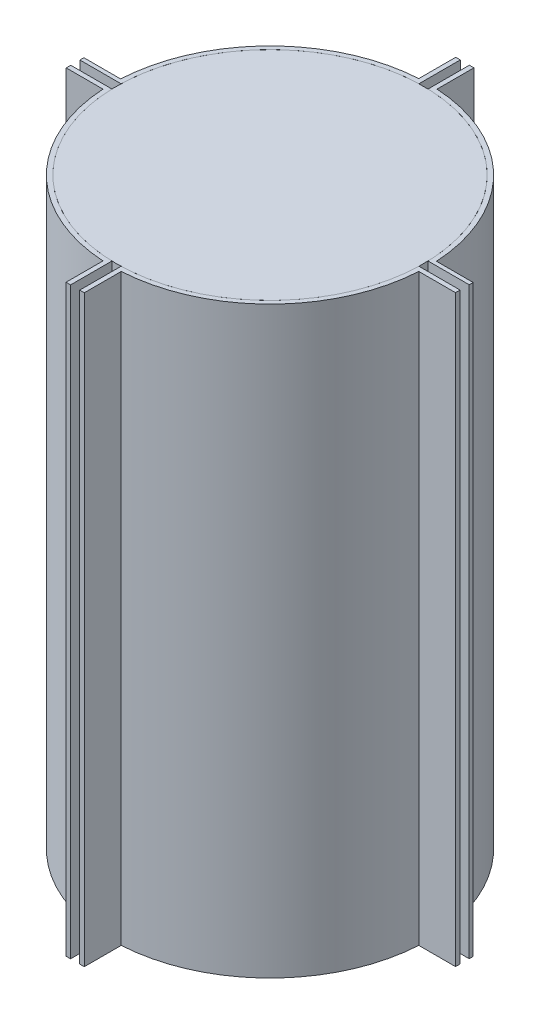
SolidWorks part; units mm, degrees
material "Alumina"
ref_plane "Front Plane" through (0, 0, 0) normal (0, 0, 1) x (1, 0, 0)
ref_plane "Top Plane" through (0, 0, 0) normal (0, 1, 0) x (1, 0, 0)
ref_plane "Right Plane" through (0, 0, 0) normal (1, 0, 0) x (0, 0, -1)
sketch "Sketch1" plane through (0, 0, 0) normal (0, 1, 0) x (1, 0, 0)
  circle A0 centre (0, 0) radius 106.934
extrude "Boss-Extrude1" add sketch "Sketch1" along normal blind 406.4
sketch "Sketch2" plane through (0, 0, 0) normal (0, 1, 0) x (1, 0, 0)
  line L1 (-110.109, 0) -> (110.109, 0) construction
  line L2 (0, 110.109) -> (0, -110.109) construction
  arc A0 (106.934, 0) -> (0, 106.934) centre (0, 0) ccw
  circle A1 centre (0, 0) radius 106.934 construction
  arc A2 (0, 106.934) -> (-106.934, 0) centre (0, 0) ccw
  arc A3 (106.934, 0) -> (0, -106.934) centre (0, 0) cw
  arc A4 (0, -106.934) -> (-106.934, 0) centre (0, 0) cw
  arc A6 (110.109, 0) -> (0, 110.109) centre (0, 0) ccw
  arc A7 (0, 110.109) -> (-110.109, 0) centre (0, 0) ccw
  arc A8 (-110.109, 0) -> (0, -110.109) centre (0, 0) ccw
  arc A9 (0, -110.109) -> (110.109, 0) centre (0, 0) ccw
  point P9 (110.109, 0)
sketch "Sketch3" plane through (0, 0, 0) normal (0, 1, 0) x (1, 0, 0)
  line L0 (0, 110.109) -> (0, -110.109) construction
  line L1 (-127, 3.175) -> (127, 3.175)
  line L2 (0, 3.175) -> (0, -3.175)
  line L3 (-127, -3.175) -> (127, -3.175)
  line L4 (127, 3.175) -> (127, -3.175)
  line L5 (-110.109, 0) -> (110.109, 0) construction
  line L6 (-127, 3.175) -> (-127, -3.175)
  line L7 (-3.175, -127) -> (3.175, -127)
  line L11 (-3.175, 0) -> (3.175, 0)
  line L12 (-3.175, -127) -> (-3.175, 127)
  line L13 (-3.175, 127) -> (3.175, 127)
  line L14 (3.175, -127) -> (3.175, 127)
  point P18 (0, 121.6953)
  dimension "D1" = 6.35
  dimension "D2" = 254
  dimension "D3" = 254
  dimension "D4" = 6.35
  dimension "D5" = 123.825
  dimension "D6" = 123.825
extrude "Boss-Extrude3" add sketch "Sketch2" along normal blind 406.4 separate body
extrude "Cut-Extrude2" cut sketch "Sketch3" along normal through all contours L3 L4 L1 L6 | L7 L14 L13 L12
sketch "Sketch5" plane through (0, 0, 0) normal (0, 1, 0) x (1, 0, 0)
  line L0 (-110.0632, 3.175) -> (-135.5208, 3.175)
  line L1 (-135.5208, 3.175) -> (-135.5208, 5.9441)
  line L4 (-135.5208, 5.9441) -> (-108.2073, 5.9441)
  line L5 (-108.2073, 5.9441) -> (-110.0632, 3.175)
  line L6 (-110.0632, -3.175) -> (-135.5208, -3.175)
  line L7 (-135.5208, -3.175) -> (-135.5208, -6.35)
  line L8 (-135.5208, -6.35) -> (-108.2073, -6.35)
  line L9 (-108.2073, -6.35) -> (-110.0632, -3.175)
  line L10 (0, 114.4986) -> (0, -118.1169) construction
  line L11 (-145.7806, 0) -> (120.2361, 0) construction
  line L12 (135.5208, -6.35) -> (108.2073, -6.35)
  line L13 (135.5208, -3.175) -> (135.5208, -6.35)
  line L14 (110.0632, -3.175) -> (135.5208, -3.175)
  line L15 (108.2073, -6.35) -> (110.0632, -3.175)
  line L16 (135.5208, 5.9441) -> (108.2073, 5.9441)
  line L17 (135.5208, 3.175) -> (135.5208, 5.9441)
  line L18 (110.0632, 3.175) -> (135.5208, 3.175)
  line L19 (108.2073, 5.9441) -> (110.0632, 3.175)
  line L20 (-3.175, 110.0632) -> (-3.175, 135.6461)
  line L21 (-3.175, 135.6461) -> (-6.3495, 135.6461)
  line L24 (-6.3495, 135.6461) -> (-6.3495, 108.3326)
  line L25 (-6.3495, 108.3326) -> (-3.175, 110.0632)
  line L26 (6.3495, 135.6461) -> (6.3495, 108.3326)
  line L27 (3.175, 135.6461) -> (6.3495, 135.6461)
  line L28 (3.175, 110.0632) -> (3.175, 135.6461)
  line L29 (6.3495, 108.3326) -> (3.175, 110.0632)
  line L30 (3.175, -135.6461) -> (6.3495, -135.6461)
  line L31 (3.175, -110.0632) -> (3.175, -135.6461)
  line L32 (6.3495, -108.3326) -> (3.175, -110.0632)
  line L33 (6.3495, -135.6461) -> (6.3495, -108.3326)
  line L34 (-6.3495, -135.6461) -> (-6.3495, -108.3326)
  line L35 (-3.175, -135.6461) -> (-6.3495, -135.6461)
  line L36 (-3.175, -110.0632) -> (-3.175, -135.6461)
  line L37 (-6.3495, -108.3326) -> (-3.175, -110.0632)
extrude "Boss-Extrude5" add sketch "Sketch5" along normal blind 406.4
